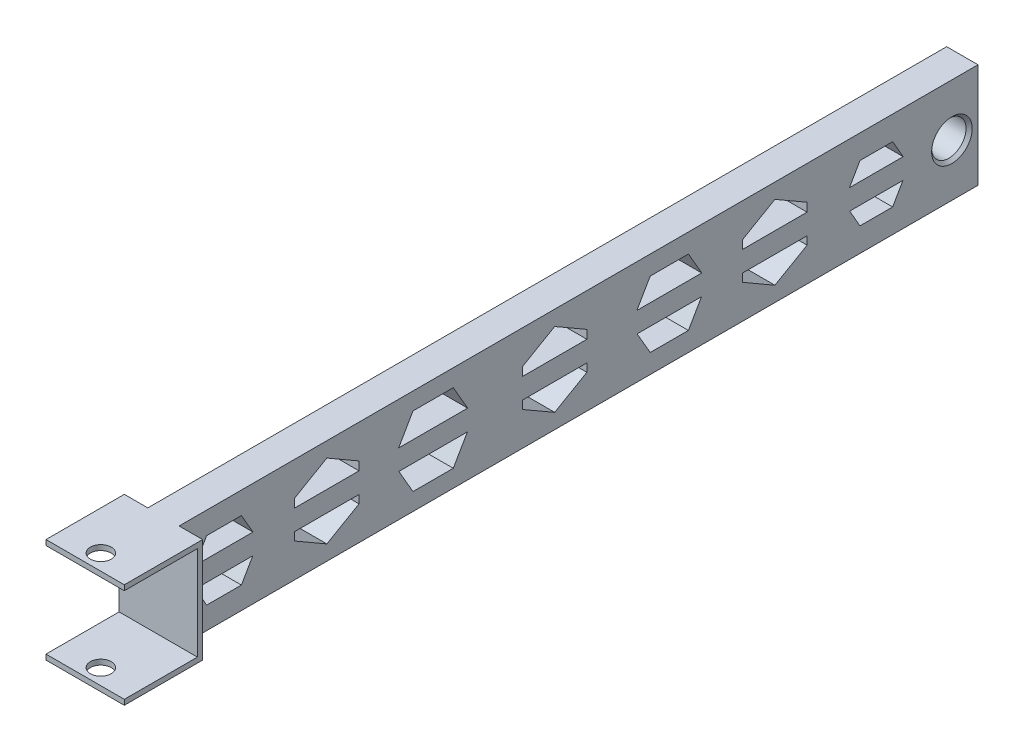
SolidWorks part; units mm, degrees
ref_plane "前视基准面" through (0, 0, 0) normal (0, 0, 1) x (1, 0, 0)
ref_plane "上视基准面" through (0, 0, 0) normal (0, 1, 0) x (1, 0, 0)
ref_plane "右视基准面" through (0, 0, 0) normal (1, 0, 0) x (0, 0, -1)
sketch "草图1" plane through (0, 0, 0) normal (0, 0, 1) x (1, 0, 0)
  line L1 (-3, -10) -> (3, -10)
  line L2 (-3, -10) -> (-3, 10)
  line L3 (-3, 10) -> (3, 10)
  line L4 (3, -10) -> (3, 10)
  line L5 (-3, -10) -> (3, 10) construction
  line L6 (-3, 10) -> (3, -10) construction
  point P0 (0, 0)
extrude "凸台-拉伸1" add sketch "草图1" along normal blind 165
sketch "草图2" plane through (3, 0, 0) normal (1, 0, 0) x (0, 0, -1)
  line L0 (0, 0) -> (-5, 0)
  point P3 (0, 0)
  point P4 (0, 0)
hole_wizard "G1/16 螺纹孔1" positions "草图3" profile "草图4" tap size "G1/16" standard "GB"
sketch "草图3" plane through (3, 0, 0) normal (1, 0, 0) x (0, 0, -1)
  point P0 (-5, 0)
sketch "草图4" plane through (3, 0, 5) normal (0, 1, 0) x (0, 0, -1)
  line L0 (0, 0) -> (0, 51.9828)
  line L1 (0, 51.9828) -> (3.3, 50)
  line L2 (3.3, 50) -> (3.3, 0.5865)
  line L3 (3.3, 0.5865) -> (3.8865, 0)
  line L5 (3.8865, 0) -> (0, 0)
  line L6 (-3.3, 0.5865) -> (-3.8865, 0) construction
  line L10 (0, 51.9828) -> (-3.3, 50) construction
  line L11 (0, -6.35) -> (0, 107.95) construction
  dimension "螺纹孔钻头直径" = 6.6
  dimension "螺纹孔钻头深度" = 50
  dimension "近端锥形沉头孔直径" = 7.773
  dimension "近端锥形沉头孔角度" = 90
  dimension "导头角度" = 118
cosmetic thread "孔螺蚊线1" parameters "D1"=15.45, "D2"=7.723
sketch "草图5" plane through (3, 0, 0) normal (1, 0, 0) x (0, 0, -1)
  line L1 (-168, -10) -> (-153, -10)
  line L2 (-168, -10) -> (-168, 10)
  line L3 (-168, 10) -> (-153, 10)
  line L4 (-153, -10) -> (-153, 10)
  line L5 (-168, -10) -> (-153, 10) construction
  line L6 (-168, 10) -> (-153, -10) construction
  point P0 (-160.5, 0)
  point P9 (0, 0)
  point P10 (0, 0)
extrude "凸台-拉伸2" add sketch "草图5" along normal blind 10 and the other way blind 15
sketch "草图6" plane through (0, -10, 0) normal (0, -1, 0) x (1, 0, 0)
  line L0 (-12, 168) -> (13, 168) construction
  line L1 (-7.5, 168) -> (7.5, 168)
  line L2 (-7.5, 168) -> (-7.5, 153)
  line L3 (-7.5, 153) -> (7.5, 153)
  line L4 (7.5, 168) -> (7.5, 153)
  line L5 (3, 153) -> (13, 153) construction
  line L6 (-7.5, 153) -> (-12, 153)
  line L7 (-12, 153) -> (-12, 168)
  line L8 (-12, 168) -> (-12, 153) construction
  line L9 (-12, 168) -> (-7.5, 168)
  line L10 (7.5, 168) -> (13, 168)
  line L11 (13, 168) -> (13, 153) construction
  line L12 (13, 168) -> (13, 153)
  line L13 (13, 153) -> (7.5, 153)
  line M4 (3, 153) -> (13, 153)
  line M5 (13, 153) -> (13, 168)
  line M6 (13, 168) -> (-12, 168)
  line M7 (-12, 168) -> (-12, 153)
  line M8 (-12, 153) -> (-3, 153)
extrude "切除-拉伸1" cut sketch "草图6" against normal blind 32 contours L4 M6 M4 M5 | L2 M6 M7 M8
sketch "草图7" plane through (0, 0, 168) normal (0, 0, 1) x (1, 0, 0)
  line L1 (-7.5, 10) -> (-7.5, -10) construction
  line L2 (7.5, 9) -> (-7.5, 9)
  line L3 (7.5, 9) -> (7.5, -9)
  line L4 (7.5, -9) -> (-7.5, -9)
  line L5 (-7.5, 9) -> (-7.5, -9)
  line L6 (7.5, 9) -> (-7.5, -9) construction
  line L7 (7.5, -9) -> (-7.5, 9) construction
  point P2 (0, 0)
extrude "切除-拉伸2" cut sketch "草图7" against normal blind 14
sketch "草图8" plane through (0, 10, 0) normal (0, 1, 0) x (1, 0, 0)
  line L0 (3, -1.1135) -> (3, -8.8865)
  line L1 (3, -8.8865) -> (3, -5)
  line L2 (3, -5) -> (0, -5)
  line L3 (0, -5) -> (0, -165)
  circle A0 centre (0, -165) radius 2
extrude "切除-拉伸3" cut sketch "草图8" against normal blind 39 contours A0
sketch "草图9" plane through (-3, 0, 0) normal (-1, 0, 0) x (0, 0, 1)
  line L0 (154, 9) -> (154, -9) construction
  line L1 (151.0541, 0) -> (147.728, 5.761)
  line L2 (147.728, 5.761) -> (141.0758, 5.761)
  line L3 (141.0758, 5.761) -> (137.7497, 0)
  line L4 (137.7497, 0) -> (141.0758, -5.761)
  line L5 (141.0758, -5.761) -> (147.728, -5.761)
  line L6 (147.728, -5.761) -> (151.0541, 0)
  line L7 (124.7114, -7.1178) -> (130.8757, -3.5589)
  line L8 (130.8757, -3.5589) -> (130.8757, 3.5589)
  line L9 (130.8757, 3.5589) -> (124.7114, 7.1178)
  line L10 (124.7114, 7.1178) -> (118.5472, 3.5589)
  line L11 (118.5472, 3.5589) -> (118.5472, -3.5589)
  line L12 (118.5472, -3.5589) -> (124.7114, -7.1178)
  line L13 (112.0723, 0) -> (108.214, 6.6827)
  line L14 (108.214, 6.6827) -> (100.4974, 6.6827)
  line L15 (100.4974, 6.6827) -> (96.6392, 0)
  line L16 (96.6392, 0) -> (100.4974, -6.6827)
  line L17 (100.4974, -6.6827) -> (108.214, -6.6827)
  line L18 (108.214, -6.6827) -> (112.0723, 0)
  line L19 (81.073, 7.1178) -> (74.9088, 3.5589)
  line L20 (74.9088, 3.5589) -> (74.9088, -3.5589)
  line L21 (74.9088, -3.5589) -> (81.073, -7.1178)
  line L22 (81.073, -7.1178) -> (87.2373, -3.5589)
  line L23 (87.2373, -3.5589) -> (87.2373, 3.5589)
  line L24 (87.2373, 3.5589) -> (81.073, 7.1178)
  line L25 (66.4382, 0) -> (62.7795, 6.3371)
  line L26 (62.7795, 6.3371) -> (55.4621, 6.3371)
  line L27 (55.4621, 6.3371) -> (51.8034, 0)
  line L28 (51.8034, 0) -> (55.4621, -6.3371)
  line L29 (55.4621, -6.3371) -> (62.7795, -6.3371)
  line L30 (62.7795, -6.3371) -> (66.4382, 0)
  line L31 (38.8981, 7.1178) -> (32.7339, 3.5589)
  line L32 (32.7339, 3.5589) -> (32.7339, -3.5589)
  line L33 (32.7339, -3.5589) -> (38.8981, -7.1178)
  line L34 (38.8981, -7.1178) -> (45.0624, -3.5589)
  line L35 (45.0624, -3.5589) -> (45.0624, 3.5589)
  line L36 (45.0624, 3.5589) -> (38.8981, 7.1178)
  line L37 (25.7268, 0) -> (22.6003, 5.4153)
  line L38 (22.6003, 5.4153) -> (16.3472, 5.4153)
  line L39 (16.3472, 5.4153) -> (13.2207, 0)
  line L40 (13.2207, 0) -> (16.3472, -5.4153)
  line L41 (16.3472, -5.4153) -> (22.6003, -5.4153)
  line L42 (22.6003, -5.4153) -> (25.7268, 0)
  line L43 (154, -1.9955) -> (11.8642, -1.9955)
  line L44 (154, -1.9955) -> (154, 1.9187)
  line L45 (154, 1.9187) -> (11.8642, 1.9187)
  line L46 (11.8642, -1.9955) -> (11.8642, 1.9187)
  circle A0 centre (144.4019, 0) radius 5.761 construction
  circle A1 centre (124.7114, 0) radius 6.1642 construction
  circle A2 centre (104.3557, 0) radius 6.6827 construction
  circle A3 centre (81.073, 0) radius 6.1642 construction
  circle A4 centre (59.1208, 0) radius 6.3371 construction
  circle A5 centre (38.8981, 0) radius 6.1642 construction
  circle A6 centre (19.4737, 0) radius 5.4153 construction
extrude "切除-拉伸4" cut sketch "草图9" against normal blind 70 contours L45 L37 L38 L39 | L42 L43 L40 L41 | L45 L35 L36 L31 L32 | L35 L43 L32 L33 L34 | L45 L25 L26 L27 | L30 L43 L28 L29 | L23 L43 L20 L21 L22 | L45 L23 L24 L19 L20 | L45 L13 L14 L15 | L18 L43 L16 L17 | L45 L8 L9 L10 L11 | L8 L43 L11 L12 L7 | L45 L1 L2 L3 | L6 L43 L4 L5
